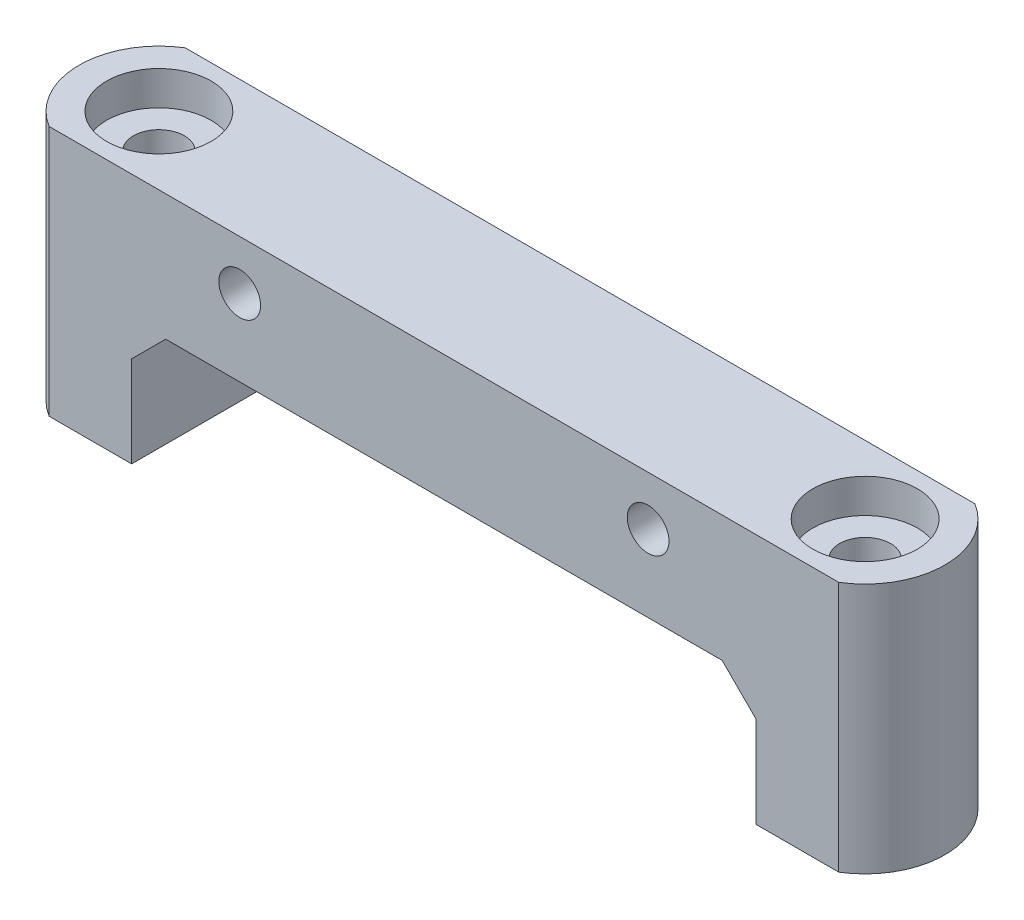
SolidWorks part; units mm, degrees
ref_plane "Front Plane" through (0, 0, 0) normal (0, 0, 1) x (1, 0, 0)
ref_plane "Top Plane" through (0, 0, 0) normal (0, 1, 0) x (1, 0, 0)
ref_plane "Right Plane" through (0, 0, 0) normal (1, 0, 0) x (0, 0, -1)
sketch "Sketch1" plane through (0, 0, 0) normal (0, 0, 1) x (1, 0, 0)
  line L0 (18.35, 7.35) -> (18.35, 0)
  line L5 (-18.25, 7.25) -> (18.25, 7.25) construction
  line L6 (-18.25, 7.25) -> (-18.25, 0) construction
  line L7 (-18.25, 0) -> (18.25, 0) construction
  line L8 (18.25, 7.25) -> (18.25, 0) construction
  line L9 (-18.35, 7.35) -> (18.35, 7.35)
  line L10 (-18.35, 7.35) -> (-18.35, 0)
  line L11 (-18.35, 0) -> (-23.2, 0)
  line L12 (-23.2, 0) -> (-23.2, 14.75)
  line L13 (-23.2, 14.75) -> (23.2, 14.75)
  line L14 (23.2, 14.75) -> (23.2, 0)
  line L15 (23.2, 0) -> (18.35, 0)
  line L16 (-23.2, 11.85) -> (23.2, 11.85) construction
  circle A0 centre (-12, 11.85) radius 1
  circle A1 centre (12, 11.85) radius 1
  point P4 (0, 0)
  point P22 (0, 14.75)
  dimension "D7" = 12
  dimension "D9" = 2
  dimension "D1" = 36.5
  dimension "D2" = 7.25
  dimension "D4" = 4.85
  dimension "D5" = 14.75
  dimension "D6" = 2.9
  dimension "D8" = 12
  dimension "D3" = 0.1
extrude "Boss-Extrude1" add sketch "Sketch1" along normal blind 8
sketch "Sketch2" plane through (0, 0, 0) normal (0, -1, 0) x (1, 0, 0)
  line L6 (-23.2, 4) -> (23.2, 4) construction
  line L7 (-23.2, 8) -> (-23.2, 0) construction
  line L8 (23.2, 8) -> (23.2, 0) construction
  circle A0 centre (-20.75, 4) radius 1.5
  circle A1 centre (20.75, 4) radius 1.5
  dimension "D1" = 3
  dimension "D2" = 41.5
  dimension "D3" = 20.75
extrude "Cut-Extrude1" cut sketch "Sketch2" against normal through all
sketch "Sketch3" plane through (0, 14.75, 0) normal (0, 1, 0) x (1, 0, 0)
  line L0 (23.2, -8) -> (23.2, 0)
  line L1 (-23.2, -8) -> (-23.2, 0)
  arc A0 (23.2, -8) -> (23.2, 0) centre (20.75, -4) ccw
  arc A1 (-23.2, 0) -> (-23.2, -8) centre (-20.75, -4) ccw
extrude "Boss-Extrude2" add sketch "Sketch3" against normal up to vertex (14.75 mm away)
sketch "Sketch5" plane through (0, 14.75, 0) normal (0, 1, 0) x (1, 0, 0)
  circle A0 centre (20.75, -4) radius 3.075
  circle A1 centre (-20.75, -4) radius 3.075
  dimension "D1" = 6.15
extrude "Cut-Extrude2" cut sketch "Sketch5" against normal blind 2 and the other way through all contours A0 | A1
chamfer "Chamfer2" distance 2 angle 45 2 edges at (-18.35, 7.35, 4) (18.35, 7.35, 4)
sketch "Sketch6" plane through (0, 0, 8) normal (0, 0, 1) x (1, 0, 0)
  circle A0 centre (-12, 11.85) radius 1.225
  circle A1 centre (12, 11.85) radius 1.225
  dimension "D1" = 2.45
extrude "Cut-Extrude3" cut sketch "Sketch6" against normal blind 5
